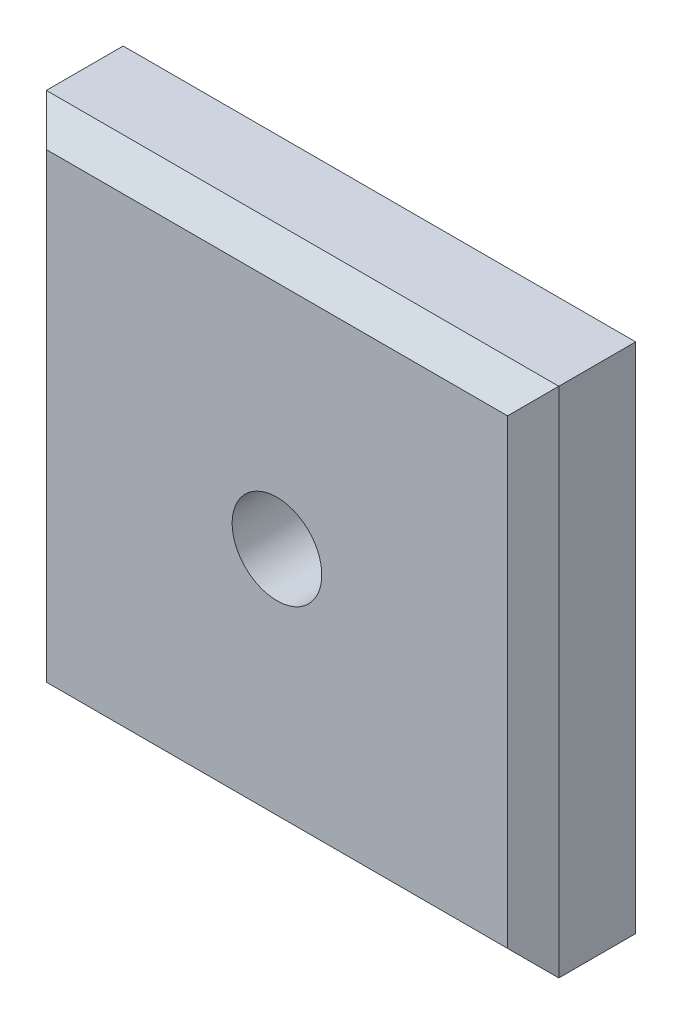
SolidWorks part; units mm, degrees
ref_plane "Front Plane" through (0, 0, 0) normal (0, 0, 1) x (1, 0, 0)
ref_plane "Top Plane" through (0, 0, 0) normal (0, 1, 0) x (1, 0, 0)
ref_plane "Right Plane" through (0, 0, 0) normal (1, 0, 0) x (0, 0, -1)
sketch "Sketch1" plane through (0, 0, 0) normal (0, 0, 1) x (1, 0, 0)
  line L1 (-20, -20) -> (20, -20)
  line L2 (-20, -20) -> (-20, 20)
  line L3 (-20, 20) -> (20, 20)
  line L4 (20, -20) -> (20, 20)
  line L5 (-20, -20) -> (20, 20) construction
  line L6 (-20, 20) -> (20, -20) construction
  point P0 (0, 0)
  dimension "D1" = 40
  dimension "D2" = 40
extrude "Boss-Extrude1" add sketch "Sketch1" along normal blind 10
hole_wizard "M8x1.0 Tapped Hole1" positions "Sketch2" profile "Sketch3" tap size "M8x1.0" standard "ANSI Metric" end condition through all
sketch "Sketch2" plane through (0, 0, 0) normal (0, 0, -1) x (-1, 0, 0)
  point P0 (0, 0)
sketch "Sketch3" plane through (0, 0, 0) normal (1, 0, 0) x (0, 1, 0)
  line L0 (0, 0) -> (0, 10)
  line L1 (0, 10) -> (3.5, 10)
  line L2 (3.5, 10) -> (3.5, 0.525)
  line L3 (3.5, 0.525) -> (4.025, 0)
  line L5 (4.025, 0) -> (0, 0)
  line L6 (-3.5, 0.525) -> (-4.025, 0) construction
  line L11 (0, -6.35) -> (0, 107.95) construction
  dimension "Thru Tap Drill Dia." = 7
  dimension "Thru Tap Drill Depth" = 10
  dimension "Near C'Sink Dia." = 8.05
  dimension "Near C'Sink Angle" = 90
cosmetic thread "Hole Thread1" parameters "D2"=8
chamfer "Chamfer1" distance 2 angle 45 8 edges at (20, 0, 10) (0, 20, 10) (-20, 0, 10) (0, -20, 10) (20, 0, 0) (0, 20, 0) (-20, 0, 0) (0, -20, 0)
